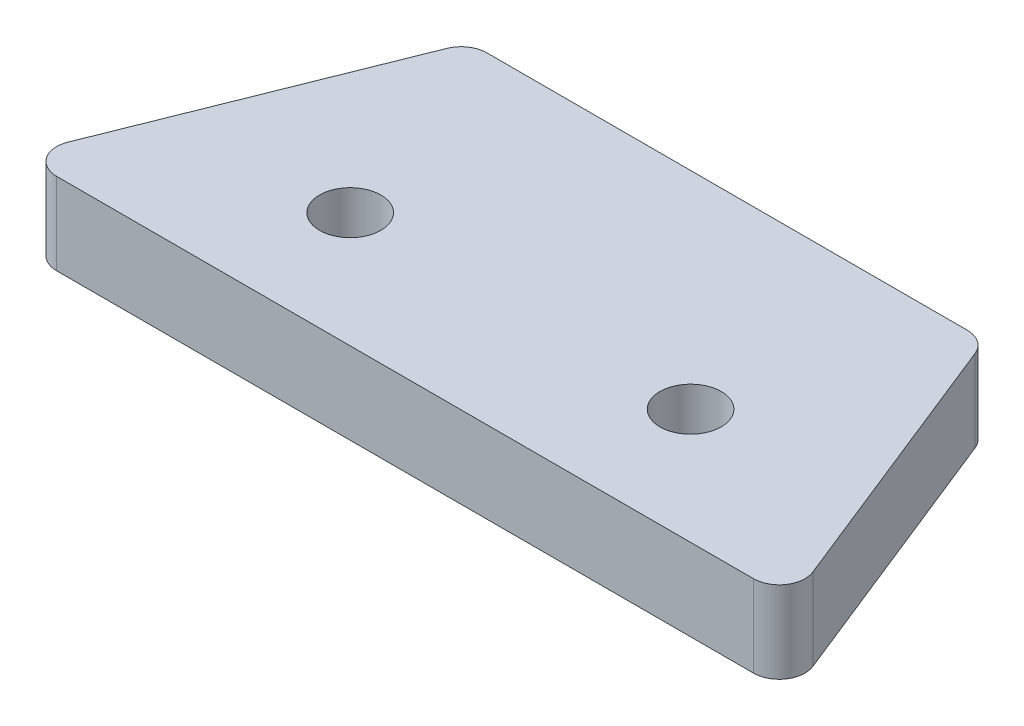
SolidWorks part; units mm, degrees
ref_plane "Front Plane" through (0, 0, 0) normal (0, 0, 1) x (1, 0, 0)
ref_plane "Top Plane" through (0, 0, 0) normal (0, 1, 0) x (1, 0, 0)
ref_plane "Right Plane" through (0, 0, 0) normal (1, 0, 0) x (0, 0, -1)
sketch "Sketch1" plane through (0, 0, 0) normal (0, 1, 0) x (1, 0, 0)
  line L0 (-20, 12.5) -> (20, 12.5)
  line L1 (20, 12.5) -> (30, -12.5)
  line L2 (30, -12.5) -> (-30, -12.5)
  line L3 (-30, -12.5) -> (-20, 12.5)
  line L4 (-13.2098, -3.5491) -> (-26.4196, -3.5491) construction
  line L5 (-13.2098, -3.5491) -> (0, -3.5491) construction
  line L6 (0, -3.5491) -> (13.2098, -3.5491) construction
  line L7 (13.2098, -3.5491) -> (26.4196, -3.5491) construction
  circle A0 centre (-13.2098, -3.5491) radius 2.38
  circle A1 centre (13.2098, -3.5491) radius 2.38
  point P2 (0, 12.5)
  point P8 (0, -12.5)
  point P9 (-25, 0)
  dimension "D4" = 4.76
  dimension "D5" = 26.4196
  dimension "D1" = 40
  dimension "D2" = 60
  dimension "D3" = 25
extrude "Boss-Extrude1" add sketch "Sketch1" along normal blind 6.35
fillet "Fillet1" radius 2 4 edges at (30, 3.175, 12.5) (20, 3.175, -12.5) (-20, 3.175, -12.5) (-30, 3.175, 12.5)
